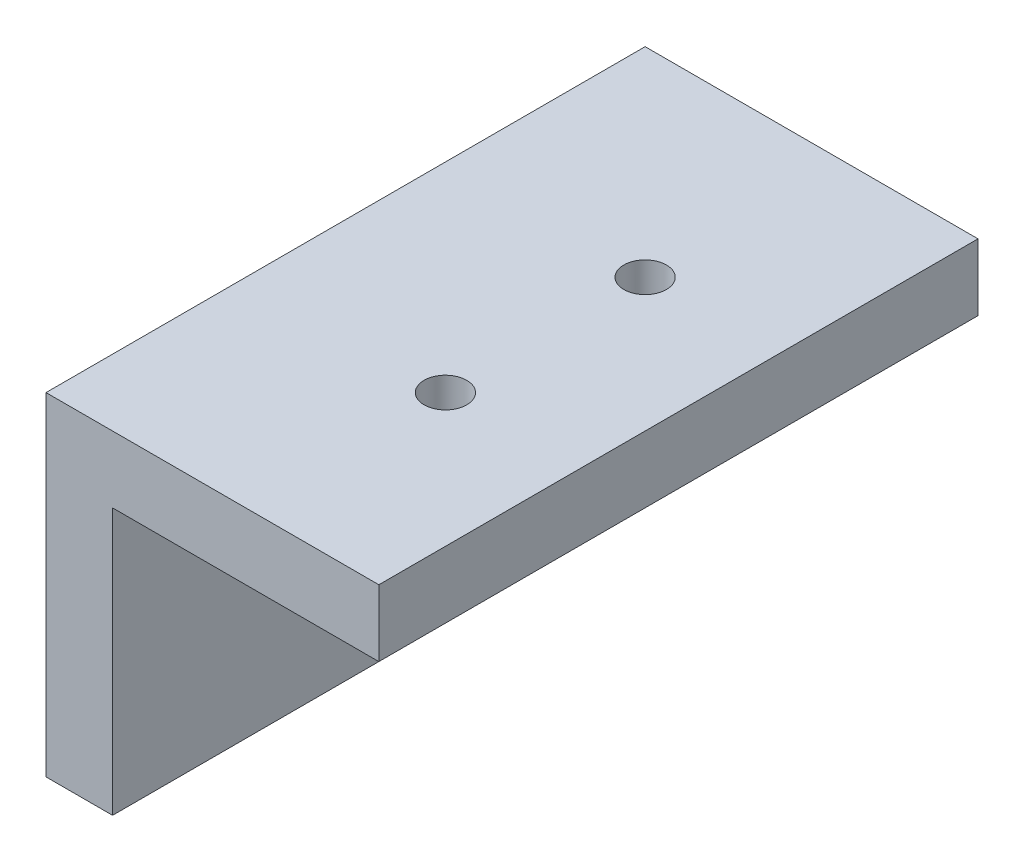
SolidWorks part; units mm, degrees
ref_plane "Front Plane" through (0, 0, 0) normal (0, 0, 1) x (1, 0, 0)
ref_plane "Top Plane" through (0, 0, 0) normal (0, 1, 0) x (1, 0, 0)
ref_plane "Right Plane" through (0, 0, 0) normal (1, 0, 0) x (0, 0, -1)
sketch "Sketch1" plane through (0, 0, 0) normal (0, 0, 1) x (1, 0, 0)
  line L0 (0, 0) -> (0, -20)
  line L1 (0, 0) -> (20, 0)
  line L2 (20, 0) -> (20, 5)
  line L3 (20, 5) -> (-5, 5)
  line L4 (-5, 5) -> (-5, -20)
  line L5 (-5, -20) -> (0, -20)
  dimension "D1" = 5
  dimension "D2" = 20
  dimension "D3" = 25
  dimension "D4" = 20
  dimension "D5" = 25
extrude "Boss-Extrude1" add sketch "Sketch1" along normal blind 45
sketch "Sketch2" plane through (0, 0, 0) normal (1, 0, 0) x (0, 0, -1)
  line L0 (-45, -10) -> (-30, -10) construction
  line L1 (-45, -20) -> (-45, 0) construction
  line L2 (-30, -10) -> (-15, -10) construction
  circle A0 centre (-30, -10) radius 1.6
  circle A1 centre (-15, -10) radius 1.6
  dimension "D3" = 3.2
  dimension "D4" = 3.2
  dimension "D1" = 15
  dimension "D2" = 15
extrude "Cut-Extrude1" cut sketch "Sketch2" against normal up to next
sketch "Sketch3" plane through (0, 0, 0) normal (0, -1, 0) x (1, 0, 0)
  line L0 (10, 45) -> (10, 30) construction
  line L1 (0, 45) -> (20, 45) construction
  line L2 (10, 30) -> (10, 15) construction
  circle A0 centre (10, 30) radius 1.6
  circle A1 centre (10, 15) radius 1.6
  dimension "D1" = 3.2
  dimension "D2" = 3.2
  dimension "D3" = 15
  dimension "D4" = 15
extrude "Cut-Extrude2" cut sketch "Sketch3" against normal up to next
sketch "Sketch4" plane through (0, 0, 0) normal (1, 0, 0) x (0, 0, -1)
  line L1 (-30, -6.5648) -> (-32.975, -8.2824)
  line L2 (-32.975, -8.2824) -> (-32.975, -11.7176)
  line L3 (-32.975, -11.7176) -> (-30, -13.4352)
  line L4 (-30, -13.4352) -> (-27.025, -11.7176)
  line L5 (-27.025, -11.7176) -> (-27.025, -8.2824)
  line L6 (-27.025, -8.2824) -> (-30, -6.5648)
  line L7 (-15, -6.5648) -> (-17.975, -8.2824)
  line L8 (-17.975, -8.2824) -> (-17.975, -11.7176)
  line L9 (-17.975, -11.7176) -> (-15, -13.4352)
  line L10 (-15, -13.4352) -> (-12.025, -11.7176)
  line L11 (-12.025, -11.7176) -> (-12.025, -8.2824)
  line L12 (-12.025, -8.2824) -> (-15, -6.5648)
  circle A0 centre (-30, -10) radius 2.975 construction
  circle A1 centre (-15, -10) radius 2.975 construction
  dimension "D1" = 5.95
  dimension "D2" = 5.95
extrude "Cut-Extrude3" cut sketch "Sketch4" against normal blind 2.5 from offset 1.25 offset against normal yes
